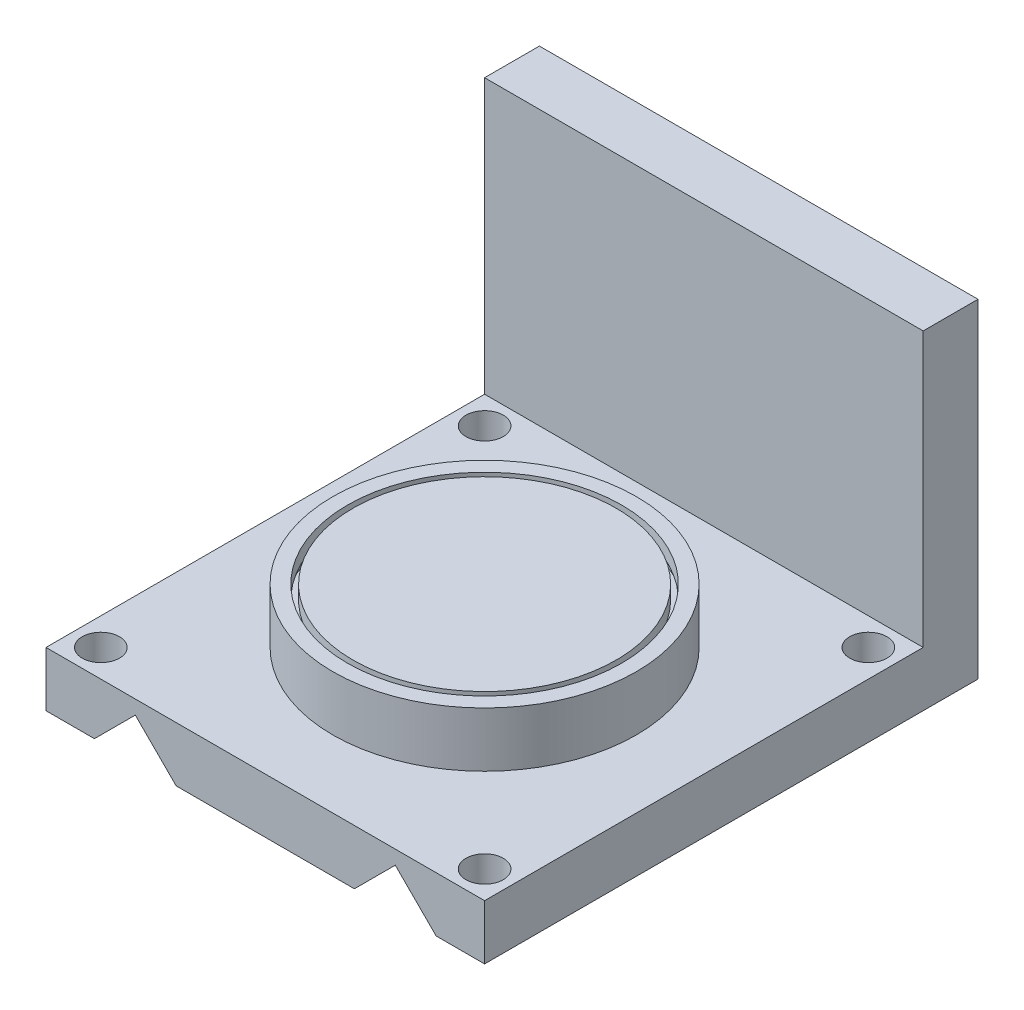
SolidWorks part; units mm, degrees
ref_plane "Front Plane" through (0, 0, 0) normal (0, 0, 1) x (1, 0, 0)
ref_plane "Top Plane" through (0, 0, 0) normal (0, 1, 0) x (1, 0, 0)
ref_plane "Right Plane" through (0, 0, 0) normal (1, 0, 0) x (0, 0, -1)
sketch "Эскиз5" plane through (0, 0, 0) normal (0, 1, 0) x (1, 0, 0)
  line L5 (-20, -20) -> (20, -20)
  line L6 (-20, -20) -> (-20, 20)
  line L7 (-20, 20) -> (20, 20)
  line L8 (20, -20) -> (20, 20)
  line L9 (-20, -20) -> (20, 20) construction
  line L10 (-20, 20) -> (20, -20) construction
  point P0 (0, 0)
extrude "Бобышка-Вытянуть2" add sketch "Эскиз5" along normal blind 5
sketch "Эскиз6" plane through (0, 0, 0) normal (0, 0, 1) x (1, 0, 0)
  line L1 (-20, 0) -> (20, 0) construction
  line L2 (8.1273, 0) -> (11.8551, 3.7279)
  line L3 (11.8551, 3.7279) -> (15.583, 0)
  line L4 (-8.1273, 0) -> (-11.8551, 3.7279)
  line L5 (-11.8551, 3.7279) -> (-15.583, 0)
  line L6 (15.583, 0) -> (8.1273, 0)
  line L7 (-8.1273, 0) -> (-15.583, 0)
  point P6 (0, 0)
extrude "Вырез-Вытянуть2" cut sketch "Эскиз6" against normal through all both and the other way through all
sketch "Эскиз7" plane through (0, 0, 0) normal (0, 1, 0) x (1, 0, 0)
  line L0 (-14.8813, -17.5) -> (-20.2569, -17.5) construction
  line L5 (-17.5, -14.9741) -> (-17.5, -19.9701) construction
  line L6 (-17.5, 20.1369) -> (-17.5, 14.842) construction
  line L7 (-14.8813, 17.5) -> (-20.2569, 17.5) construction
  line L8 (17.5, 20.0205) -> (17.5, 14.842) construction
  line L9 (20, 17.5) -> (14.8492, 17.5) construction
  line L10 (20, -20) -> (20, 20) construction
  line L11 (20, -17.5) -> (14.8492, -17.5) construction
  line L12 (17.5, -19.9701) -> (17.5, -14.9741) construction
  circle A0 centre (-17.5, -17.5) radius 1.7
  circle A1 centre (-17.5, 17.5) radius 1.7
  circle A2 centre (17.5, 17.5) radius 1.7
  circle A3 centre (17.5, -17.5) radius 1.7
  point P0 (0, 0)
extrude "Вырез-Вытянуть4" cut sketch "Эскиз7" against normal through all and the other way through all
sketch "Эскиз8" plane through (0, 5, 0) normal (0, 1, 0) x (1, 0, 0)
  line L0 (-21.2623, 0) -> (21.338, 0) construction
  line L1 (0, 21.7163) -> (0, -21.2623) construction
  circle A0 centre (0, 0) radius 13.8362
extrude "Бобышка-Вытянуть3" add sketch "Эскиз8" along normal blind 5
ref_point "Точка6"
sketch "Эскиз9" plane through (0, 10, 0) normal (0, 1, 0) x (1, 0, 0)
  circle A0 centre (0, 0) radius 12.5
  circle A1 centre (0, 0) radius 12
extrude "Вырез-Вытянуть5" cut sketch "Эскиз9" against normal blind 2.5
ref_point "Точка10"
sketch "Эскиз11" plane through (0, 7.5, 0) normal (0, 1, 0) x (1, 0, 0)
  circle A0 centre (0, 0) radius 13
  circle A1 centre (0, 0) radius 11.5
extrude "Вырез-Вытянуть6" cut sketch "Эскиз11" along normal blind 1.25
sketch "Эскиз13" plane through (0, 0, 0) normal (0, 1, 0) x (1, 0, 0)
  line L1 (-20, 20) -> (20, 20)
  line L2 (-20, 20) -> (-20, 25)
  line L3 (-20, 25) -> (20, 25)
  line L4 (20, 20) -> (20, 25)
  line L5 (-20, 20) -> (20, 25) construction
  line L6 (-20, 25) -> (20, 20) construction
  point P4 (0, 22.5)
extrude "Бобышка-Вытянуть5" add sketch "Эскиз13" along normal blind 30
ref_point "Точка12"
sketch "Эскиз15" plane through (0, 0, 0) normal (0, 0, 1) x (1, 0, 0)
  line L0 (-20, 5) -> (-4, 30)
  line L1 (-20, 30) -> (20, 30) construction
  line L2 (20, 5) -> (4, 30)
  line L3 (-20, 5) -> (-20, 30)
  line L4 (-20, 30) -> (-4, 30)
  line L5 (4, 30) -> (20, 30)
  line L6 (20, 30) -> (20, 5)
